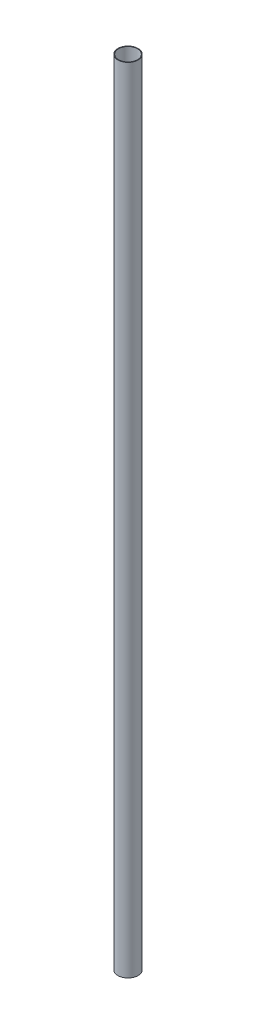
SolidWorks part; units mm, degrees
ref_plane "Front Plane" through (0, 0, 0) normal (0, 0, 1) x (1, 0, 0)
ref_plane "Top Plane" through (0, 0, 0) normal (0, 1, 0) x (1, 0, 0)
ref_plane "Right Plane" through (0, 0, 0) normal (1, 0, 0) x (0, 0, -1)
sketch "Sketch1" plane through (0, 0, 0) normal (0, 1, 0) x (1, 0, 0)
  circle A0 centre (0, 0) radius 20.955
  circle A1 centre (0, 0) radius 19.685
  dimension "D1" = 41.91
  dimension "D2" = 39.37
extrude "Boss-Extrude1" add sketch "Sketch1" along normal blind 1651
